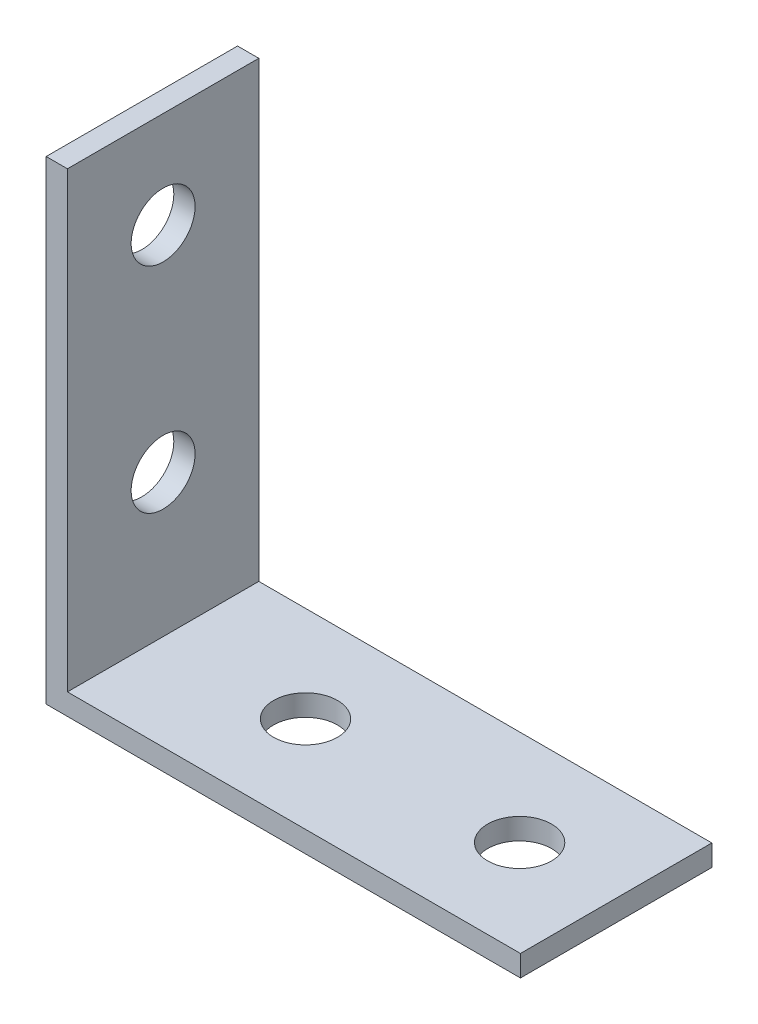
SolidWorks part; units mm, degrees
ref_plane "Front Plane" through (0, 0, 0) normal (0, 0, 1) x (1, 0, 0)
ref_plane "Top Plane" through (0, 0, 0) normal (0, 1, 0) x (1, 0, 0)
ref_plane "Right Plane" through (0, 0, 0) normal (1, 0, 0) x (0, 0, -1)
sketch "Sketch2" plane through (0, 0, 0) normal (0, 1, 0) x (1, 0, 0)
  line L0 (0, 8.01) -> (39.7, 8.01) construction
  line L1 (0, 0) -> (39.7, 0)
  line L2 (0, 0) -> (0, 16.02)
  line L3 (0, 16.02) -> (39.7, 16.02)
  line L4 (39.7, 0) -> (39.7, 16.02)
  line L5 (13.7, 0) -> (13.7, 16.02) construction
  line L6 (31.62, 0) -> (31.62, 16.02) construction
  circle A0 centre (13.7, 8.01) radius 2.675
  circle A1 centre (31.62, 8.01) radius 2.675
  dimension "D4" = 5.35
  dimension "D1" = 39.7
  dimension "D2" = 16.02
  dimension "D3" = 13.7
  dimension "D5" = 31.62
extrude "Boss-Extrude1" add sketch "Sketch2" along normal blind 1.78
sketch "Sketch3" plane through (0, 1.78, 0) normal (0, 1, 0) x (1, 0, 0)
  line L0 (39.7, 16.02) -> (0, 16.02) construction
  line L1 (0, 0) -> (1.78, 0)
  line L2 (0, 0) -> (0, 16.02)
  line L3 (0, 16.02) -> (1.78, 16.02)
  line L4 (1.78, 0) -> (1.78, 16.02)
  line L5 (0, 0) -> (1.78, 16.02) construction
  line L6 (0, 16.02) -> (1.78, 0) construction
  point P4 (0.89, 8.01)
  dimension "D1" = 1.78
extrude "Boss-Extrude2" add sketch "Sketch3" along normal blind 37.92
sketch "Sketch4" plane through (1.78, 0, 0) normal (1, 0, 0) x (0, 0, -1)
  line L0 (8.01, 1.78) -> (8.01, 39.7) construction
  line L1 (0, 1.78) -> (16.02, 1.78) construction
  line L2 (0, 39.7) -> (16.02, 39.7) construction
  line L3 (16.02, 31.62) -> (0, 31.62) construction
  line L4 (16.02, 39.7) -> (16.02, 1.78) construction
  line L5 (0, 39.7) -> (0, 1.78) construction
  line L6 (16.02, 13.7) -> (0, 13.7) construction
  circle A0 centre (8.01, 13.7) radius 2.675
  circle A1 centre (8.01, 31.62) radius 2.675
  dimension "D3" = 5.35
  dimension "D1" = 29.84
  dimension "D2" = 11.92
extrude "Cut-Extrude1" cut sketch "Sketch4" against normal blind 37.92
